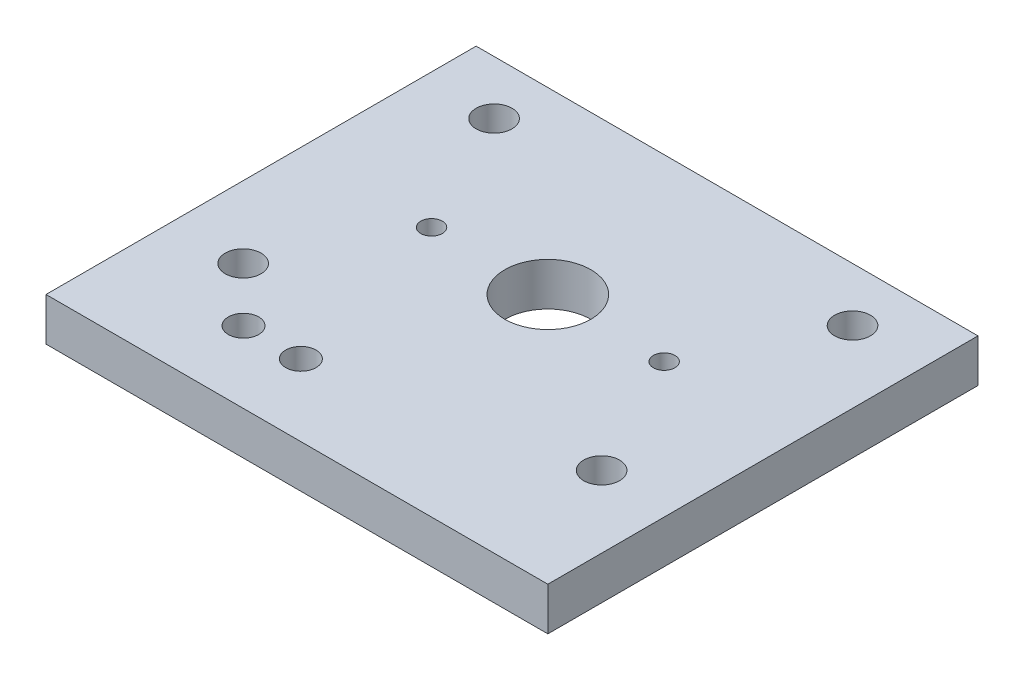
SolidWorks part; units mm, degrees
ref_plane "Front Plane" through (0, 0, 0) normal (0, 0, 1) x (1, 0, 0)
ref_plane "Top Plane" through (0, 0, 0) normal (0, 1, 0) x (1, 0, 0)
ref_plane "Right Plane" through (0, 0, 0) normal (1, 0, 0) x (0, 0, -1)
sketch "Sketch1" plane through (0, 0, 0) normal (0, 1, 0) x (1, 0, 0)
  line L0 (0, -55) -> (0, 55) construction
  line L5 (-55, 0) -> (55, 0) construction
  line L6 (-35, 25) -> (35, 25)
  line L7 (-35, 25) -> (-35, -25)
  line L8 (-35, -25) -> (35, -25)
  line L9 (35, 25) -> (35, -25)
  line L10 (-35, 25) -> (35, -25) construction
  line L11 (-35, -25) -> (35, 25) construction
  line L12 (-17.4501, -25) -> (-9.4501, -25) construction
  line L13 (-17.4501, -21) -> (-9.4501, -21) construction
  line L14 (-17.4501, -29) -> (-9.4501, -29) construction
  line L16 (-35, -25) -> (35, -25)
  line L17 (-35, -25) -> (-35, -35)
  line L18 (-35, -35) -> (35, -35)
  line L19 (35, -25) -> (35, -35)
  circle A0 centre (0, 0) radius 6
  circle A1 centre (0, 0) radius 16.22 construction
  circle A2 centre (-16.22, 0) radius 1.5
  circle A3 centre (16.22, 0) radius 1.5
  circle A4 centre (-25, 17.5) radius 2.5
  circle A5 centre (25, 17.5) radius 2.5
  circle A6 centre (25, -17.5) radius 2.5
  circle A7 centre (-25, -17.5) radius 2.5
  circle A8 centre (-9.4501, -25) radius 2.125
  circle A9 centre (-17.4501, -25) radius 2.125
  arc A10 (-17.4501, -21) -> (-17.4501, -29) centre (-17.4501, -25) ccw construction
  arc A11 (-9.4501, -29) -> (-9.4501, -21) centre (-9.4501, -25) ccw construction
  point P27 (-13.4501, -25)
  dimension "D1" = 12
  dimension "D2" = 32.44
  dimension "D3" = 3
  dimension "D4" = 5
  dimension "D10" = 4.25
  dimension "D12" = 4
  dimension "D5" = 50
  dimension "D6" = 25
  dimension "D7" = 70
  dimension "D8" = 17.5
  dimension "D9" = 8
  dimension "D11" = 25
  dimension "D13" = 10
extrude "Boss-Extrude1" add sketch "Sketch1" along normal blind 6 contours A9 L8 A8 L9 L6 L7 A5 A4 A0 A2 A3 A6 A7 | A9 L8 L17 L18 L19 A8
